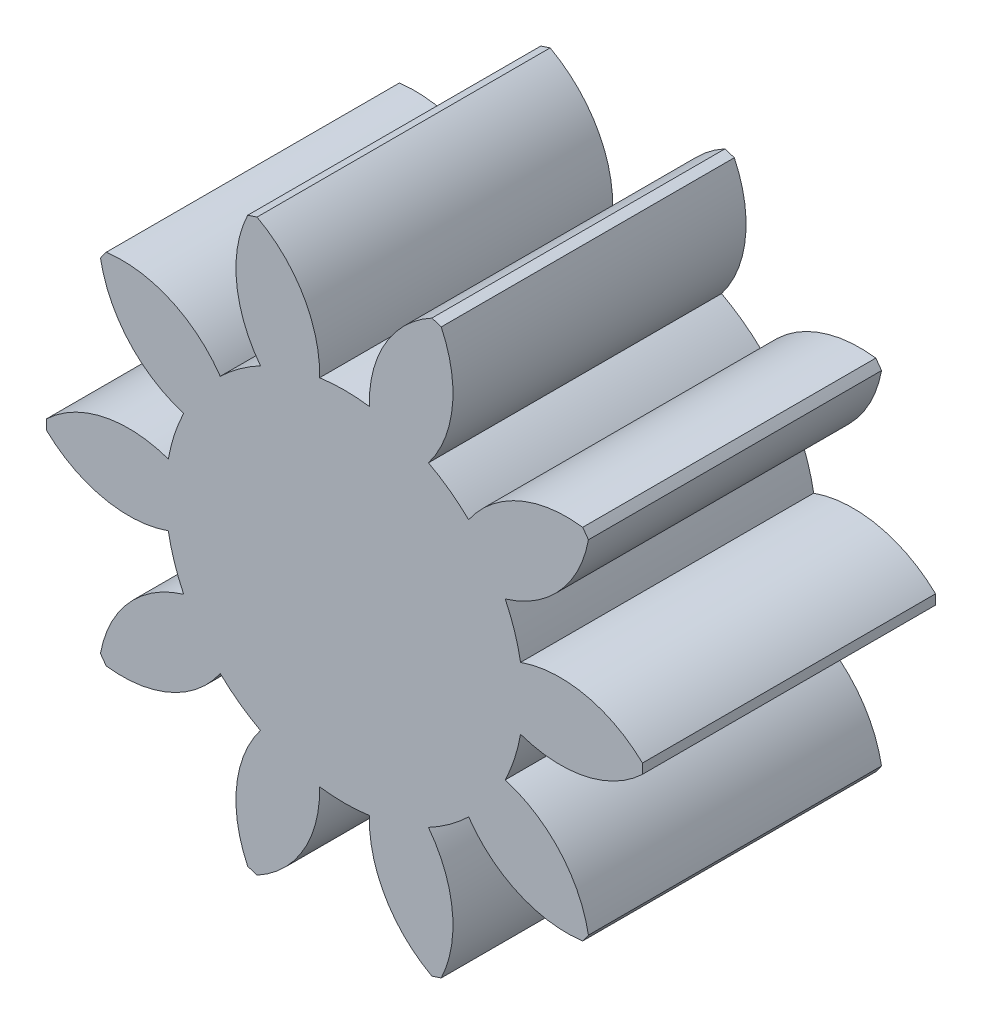
SolidWorks part; units mm, degrees
ref_plane "Front Plane" through (0, 0, 0) normal (0, 0, 1) x (1, 0, 0)
ref_plane "Top Plane" through (0, 0, 0) normal (0, 1, 0) x (1, 0, 0)
ref_plane "Right Plane" through (0, 0, 0) normal (1, 0, 0) x (0, 0, -1)
sketch "Sketch1" plane through (0, 0, 0) normal (0, 0, 1) x (1, 0, 0)
  circle A0 centre (0, 0) radius 15
  dimension "D1" = 30
extrude "Boss-Extrude1" add sketch "Sketch1" along normal blind 14.75
sketch "Sketch2" plane through (0, 0, 14.75) normal (0, 0, 1) x (1, 0, 0)
  arc A0 (-1.25, 8.9128) -> (1.25, 8.9128) centre (0, 0) cw
  arc A1 (-4.4, 14.3402) -> (4.4, 14.3402) centre (0, 0) cw
  circle A2 centre (0, 0) radius 15 construction
  arc A3 (-4.4, 14.3402) -> (-1.25, 8.9128) centre (-7.2482, 9.0593) cw
  arc A4 (1.25, 8.9128) -> (4.4, 14.3402) centre (7.2482, 9.0593) cw
  point P10 (0, 9)
  point P11 (0, 15)
  dimension "D1" = 9
  dimension "D2" = 6
  dimension "D3" = 8.8
  dimension "D4" = 2.5
extrude "Cut-Extrude1" cut sketch "Sketch2" against normal through all
pattern_circular "CirPattern1" count 10 over 360 about axis through (0, 0, 0) along (0, 0, 1) of "Cut-Extrude1"
sketch "Sketch3" plane through (0, 0, 14.75) normal (0, 0, 1) x (1, 0, 0)
  circle A0 centre (0, 0) radius 2.5
  dimension "D1" = 5
